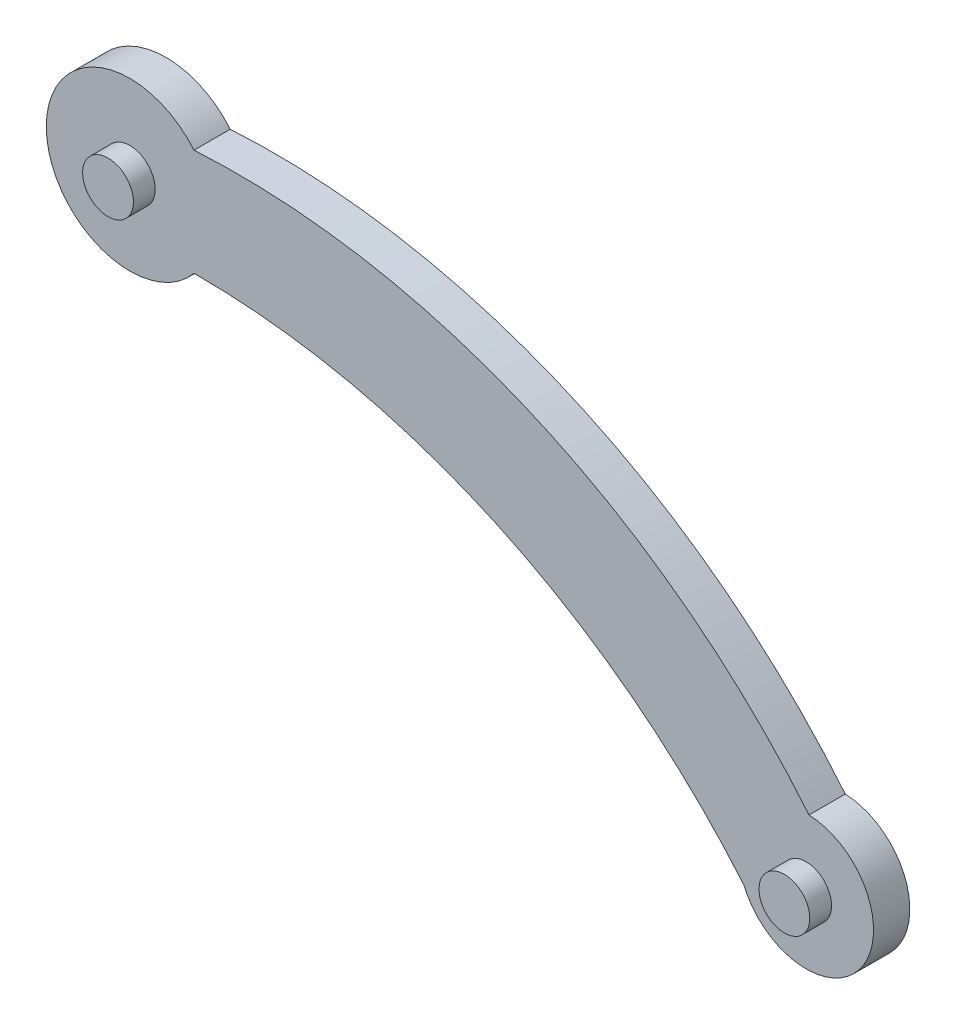
SolidWorks part; units mm, degrees
ref_plane "Front Plane" through (0, 0, 0) normal (0, 0, 1) x (1, 0, 0)
ref_plane "Top Plane" through (0, 0, 0) normal (0, 1, 0) x (1, 0, 0)
ref_plane "Right Plane" through (0, 0, 0) normal (1, 0, 0) x (0, 0, -1)
sketch "Sketch1" plane through (0, 0, 0) normal (0, 0, 1) x (1, 0, 0)
  arc A1 (-43.09, 39.0626) -> (126.4556, -34.8773) centre (-30.8821, -164.3) cw
  arc A3 (108.5071, -60.5763) -> (126.4556, -34.8773) centre (125.6684, -53.4447) ccw
  arc A4 (108.5071, -60.5763) -> (-43.09, 9.6507) centre (-42.2501, -187.274) ccw
  arc A5 (-43.09, 39.0626) -> (-43.09, 9.6507) centre (-60.7953, 24.3567) ccw
extrude "Boss-Extrude1" add sketch "Sketch1" along normal blind 10
sketch "Sketch2" plane through (0, 0, 10) normal (0, 0, 1) x (1, 0, 0)
  circle A1 centre (125.6684, -53.4447) radius 7
  circle A2 centre (-60.7953, 24.3567) radius 7
extrude "Boss-Extrude2" add sketch "Sketch2" along normal blind 6
